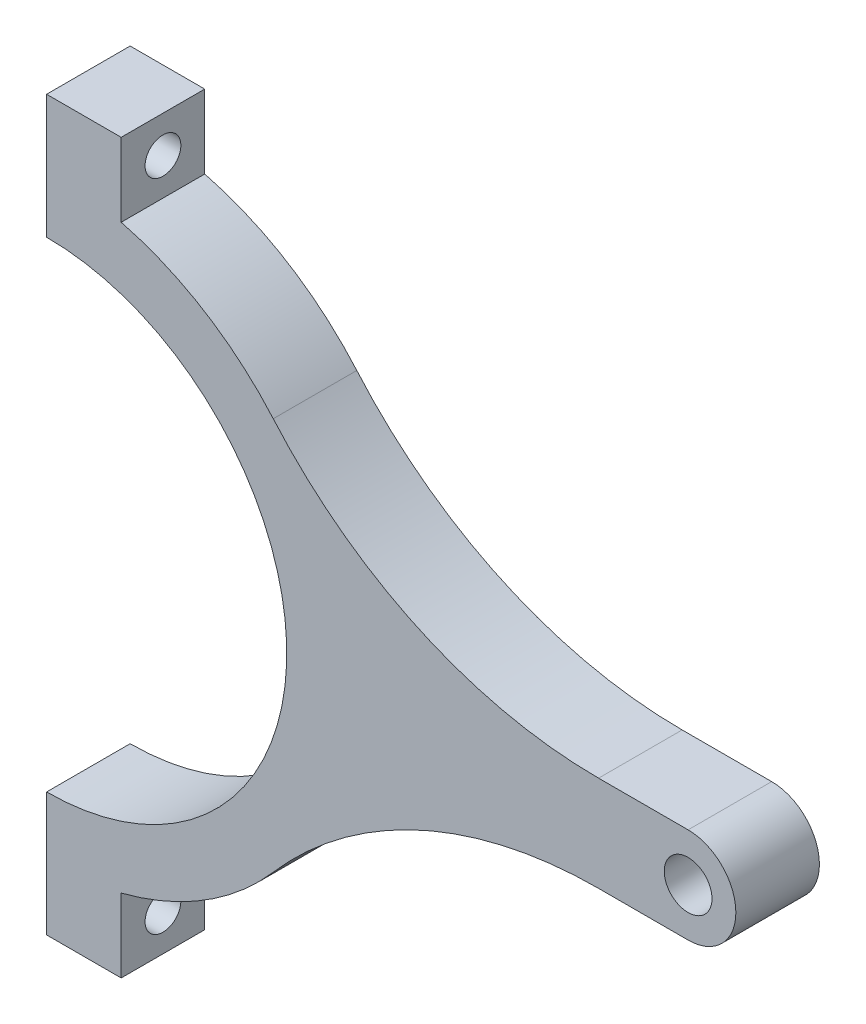
SolidWorks part; units mm, degrees
ref_plane "Front Plane" through (0, 0, 0) normal (0, 0, 1) x (1, 0, 0)
ref_plane "Top Plane" through (0, 0, 0) normal (0, 1, 0) x (1, 0, 0)
ref_plane "Right Plane" through (0, 0, 0) normal (1, 0, 0) x (0, 0, -1)
sketch "Sketch1" plane through (0, 0, 0) normal (0, 0, 1) x (1, 0, 0)
  line L0 (0, -122) -> (0, -80.5)
  line L1 (0, 122) -> (25, 122)
  line L2 (25, 122) -> (25, 97.3409)
  line L3 (0, -122) -> (25, -122)
  line L4 (25, -122) -> (25, -97.3409)
  line L5 (0, 80.5) -> (0, 122)
  line L6 (215, 16) -> (185, 16)
  line L7 (215, -16) -> (185, -16)
  arc A0 (0, 80.5) -> (0, -80.5) centre (0, 0) cw
  arc A1 (25, 97.3409) -> (75.9607, 65.8044) centre (0, 0) cw
  circle A2 centre (215, 0) radius 8
  arc A3 (215, -16) -> (215, 16) centre (215, 0) ccw
  arc A4 (75.9607, 65.8044) -> (185, 16) centre (185, 160.2648) ccw
  arc A5 (75.9607, -65.8044) -> (185, -16) centre (185, -160.2648) cw
  arc A6 (75.9607, -65.8044) -> (25, -97.3409) centre (0, 0) cw
  dimension "D1" = 80.5
  dimension "D2" = 100.5
  dimension "D7" = 32
  dimension "D8" = 16
  dimension "D3" = 244
  dimension "D4" = 122
  dimension "D5" = 25
  dimension "D6" = 25
  dimension "D9" = 215
  dimension "D10" = 30
extrude "Boss-Extrude1" add sketch "Sketch1" along normal blind 28
sketch "Sketch2" plane through (0, 0, 0) normal (-1, 0, 0) x (0, 0, 1)
  line L1 (28, 122) -> (0, 122) construction
  line L2 (28, -122) -> (0, -122) construction
  circle A0 centre (14, 109.7) radius 6
  circle A1 centre (14, -109.7) radius 6
  point P9 (14, -122)
  dimension "D1" = 12
  dimension "D4" = 12.3
  dimension "D2" = 14
  dimension "D3" = 12.3
extrude "Cut-Extrude1" cut sketch "Sketch2" against normal blind 28
